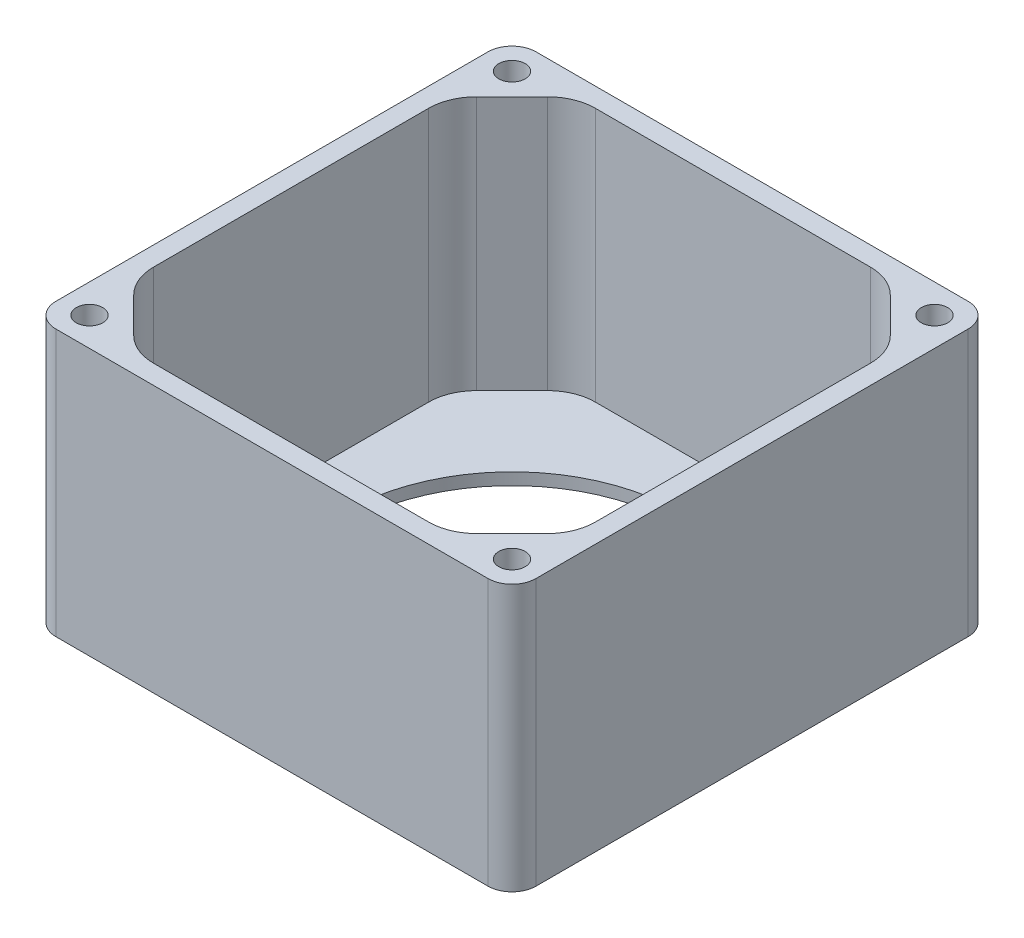
SolidWorks part; units mm, degrees
ref_plane "Front Plane" through (0, 0, 0) normal (0, 0, 1) x (1, 0, 0)
ref_plane "Top Plane" through (0, 0, 0) normal (0, 1, 0) x (1, 0, 0)
ref_plane "Right Plane" through (0, 0, 0) normal (1, 0, 0) x (0, 0, -1)
sketch "Sketch1" plane through (0, 0, 0) normal (0, 1, 0) x (1, 0, 0)
  line L1 (-57.15, 63.5) -> (57.15, 63.5)
  line L2 (-63.5, 57.15) -> (-63.5, -57.15)
  line L3 (-57.15, -63.5) -> (57.15, -63.5)
  line L4 (63.5, 57.15) -> (63.5, -57.15)
  line L5 (-49.403, 53.594) -> (49.403, 53.594) construction
  line L6 (-49.403, 53.594) -> (-49.403, -53.594) construction
  line L7 (-49.403, -53.594) -> (49.403, -53.594) construction
  line L8 (49.403, 53.594) -> (49.403, -53.594) construction
  circle A0 centre (0, 0) radius 44.45
  circle A1 centre (-57.15, 53.975) radius 3.25
  circle A2 centre (57.15, 53.975) radius 3.25
  circle A3 centre (57.15, -53.975) radius 3.25
  circle A4 centre (-57.15, -53.975) radius 3.25
  arc A5 (-63.5, -57.15) -> (-57.15, -63.5) centre (-57.15, -57.15) ccw
  arc A6 (57.15, -63.5) -> (63.5, -57.15) centre (57.15, -57.15) ccw
  arc A7 (57.15, 63.5) -> (63.5, 57.15) centre (57.15, 57.15) cw
  arc A8 (-57.15, 63.5) -> (-63.5, 57.15) centre (-57.15, 57.15) ccw
  point P21 (-63.5, -63.5)
  point P26 (63.5, 63.5)
  point P29 (-63.5, 63.5)
  dimension "D1" = 88.9
  dimension "D10" = 6.5
  dimension "D11" = 6.5
  dimension "D12" = 6.5
  dimension "D13" = 6.5
  dimension "D22" = 6.35
  dimension "D2" = 127
  dimension "D3" = 127
  dimension "D4" = 63.5
  dimension "D5" = 63.5
  dimension "D6" = 107.188
  dimension "D7" = 98.806
  dimension "D8" = 19.812
  dimension "D9" = 14.097
  dimension "D14" = 9.525
  dimension "D15" = 6.35
  dimension "D16" = 9.525
  dimension "D17" = 6.35
  dimension "D18" = 6.35
  dimension "D19" = 9.525
  dimension "D20" = 9.525
  dimension "D21" = 6.35
extrude "Boss-Extrude1" add sketch "Sketch1" along normal blind 3.175
sketch "Sketch3" plane through (0, 3.175, 0) normal (0, 1, 0) x (1, 0, 0)
  line L0 (-54.7003, 45.359) -> (-45.359, 54.7003)
  line L1 (45.359, 54.7003) -> (54.7003, 45.359)
  line L2 (54.7003, -45.359) -> (45.359, -54.7003)
  line L3 (-45.359, -54.7003) -> (-54.7003, -45.359)
  line L4 (-57.15, -63.5) -> (57.15, -63.5)
  line L5 (63.5, -57.15) -> (63.5, 57.15)
  line L6 (57.15, 63.5) -> (-57.15, 63.5)
  line L7 (-63.5, 57.15) -> (-63.5, -57.15)
  line L8 (-57.15, -63.5) -> (57.15, -63.5)
  line L9 (63.5, -57.15) -> (63.5, 57.15)
  line L10 (57.15, 63.5) -> (-57.15, 63.5)
  line L11 (-63.5, 57.15) -> (-63.5, -57.15)
  line L12 (-36.3787, 58.42) -> (36.3787, 58.42)
  line L13 (58.42, -36.3787) -> (58.42, 36.3787)
  line L14 (-36.3787, -58.42) -> (36.3787, -58.42)
  line L15 (-58.42, -36.3787) -> (-58.42, 36.3787)
  arc A0 (36.3787, 58.42) -> (45.359, 54.7003) centre (36.3787, 45.72) cw
  arc A1 (58.42, 36.3787) -> (54.7003, 45.359) centre (45.72, 36.3787) ccw
  arc A2 (58.42, -36.3787) -> (54.7003, -45.359) centre (45.72, -36.3787) cw
  arc A3 (36.3787, -58.42) -> (45.359, -54.7003) centre (36.3787, -45.72) ccw
  arc A4 (-63.5, -57.15) -> (-57.15, -63.5) centre (-57.15, -57.15) ccw
  arc A5 (57.15, -63.5) -> (63.5, -57.15) centre (57.15, -57.15) ccw
  arc A6 (63.5, 57.15) -> (57.15, 63.5) centre (57.15, 57.15) ccw
  arc A7 (-57.15, 63.5) -> (-63.5, 57.15) centre (-57.15, 57.15) ccw
  arc A8 (-63.5, -57.15) -> (-57.15, -63.5) centre (-57.15, -57.15) ccw
  arc A9 (57.15, -63.5) -> (63.5, -57.15) centre (57.15, -57.15) ccw
  arc A10 (63.5, 57.15) -> (57.15, 63.5) centre (57.15, 57.15) ccw
  arc A11 (-57.15, 63.5) -> (-63.5, 57.15) centre (-57.15, 57.15) ccw
  arc A12 (-36.3787, -58.42) -> (-45.359, -54.7003) centre (-36.3787, -45.72) cw
  arc A13 (-58.42, -36.3787) -> (-54.7003, -45.359) centre (-45.72, -36.3787) ccw
  arc A14 (-58.42, 36.3787) -> (-54.7003, 45.359) centre (-45.72, 36.3787) cw
  arc A15 (-36.3787, 58.42) -> (-45.359, 54.7003) centre (-36.3787, 45.72) ccw
  dimension "D2" = 12.7
  dimension "D3" = 72.7574
  dimension "D4" = 72.7574
  dimension "D5" = 72.7574
  dimension "D6" = 72.7574
  dimension "D7" = 135
  dimension "D8" = 135
  dimension "D9" = 135
  dimension "D10" = 135
  dimension "D11" = 180
  dimension "D12" = 180
  dimension "D13" = 180
  dimension "D14" = 13.2106
  dimension "D15" = 13.2106
  dimension "D16" = 8.7997
  dimension "D17" = 11.791
  dimension "D1" = 0
extrude "Boss-Extrude2" add sketch "Sketch3" along normal blind 67.31
hole_wizard "CBORE for M6 SHCS2" positions "Sketch8" profile "Sketch9" counterbore size "M6" standard "ANSI Metric" end condition through all
sketch "Sketch8" plane through (0, 0, 0) normal (0, -1, 0) x (-1, 0, 0)
  line L0 (57.15, -63.5) -> (-57.15, -63.5) construction
  line L1 (63.5, 57.15) -> (63.5, -57.15) construction
  line L2 (-63.5, -57.15) -> (-63.5, 57.15) construction
  line L3 (-57.15, 63.5) -> (57.15, 63.5) construction
  point P0 (-55.88, 55.88)
  point P4 (55.88, 55.88)
  point P6 (55.88, -55.88)
  point P10 (-55.88, -55.88)
  dimension "D1" = 7.62
  dimension "D2" = 7.62
  dimension "D3" = 7.62
  dimension "D4" = 7.62
  dimension "D5" = 7.62
  dimension "D6" = 7.62
  dimension "D7" = 7.62
  dimension "D8" = 7.62
sketch "Sketch9" plane through (55.88, 0, -55.88) normal (1, 0, 0) x (0, 0, -1)
  line L0 (0, 0) -> (0, 70.485)
  line L1 (0, 70.485) -> (3.5, 70.485)
  line L3 (3.5, 70.485) -> (3.5, 31.4)
  line L4 (5.5, 31.4) -> (3.5, 31.4)
  line L5 (5.5, 31.4) -> (5.5, 0.025)
  line L6 (5.5, 0.025) -> (5.525, 0)
  line L7 (5.525, 0) -> (0, 0)
  line L8 (-5.5, 0.025) -> (-5.525, 0) construction
  line L11 (0, -6.35) -> (0, 107.95) construction
  dimension "Thru Hole Dia." = 7
  dimension "Thru Hole Depth" = 70.485
  dimension "C'Bore Dia." = 11
  dimension "C'Bore Depth" = 31.4
  dimension "Near C'Sink Dia." = 11.05
  dimension "Near C'Sink Angle" = 90
equation "\"D4@Sketch1\"=\"D3@Sketch1\"/2"
equation "\"D5@Sketch1\"=\"D2@Sketch1\"/2"
equation "\"D8@Sketch1\"=\"D2@Sketch1\"-\"D6@Sketch1\""
equation "\"D9@Sketch1\"=(\"D3@Sketch1\"-\"D7@Sketch1\")/2"
equation "\"D10@Sketch1\"=6.5/25.4"
equation "\"D11@Sketch1\"=\"D10@Sketch1\""
equation "\"D12@Sketch1\"=\"D10@Sketch1\""
equation "\"D13@Sketch1\"=\"D10@Sketch1\""
